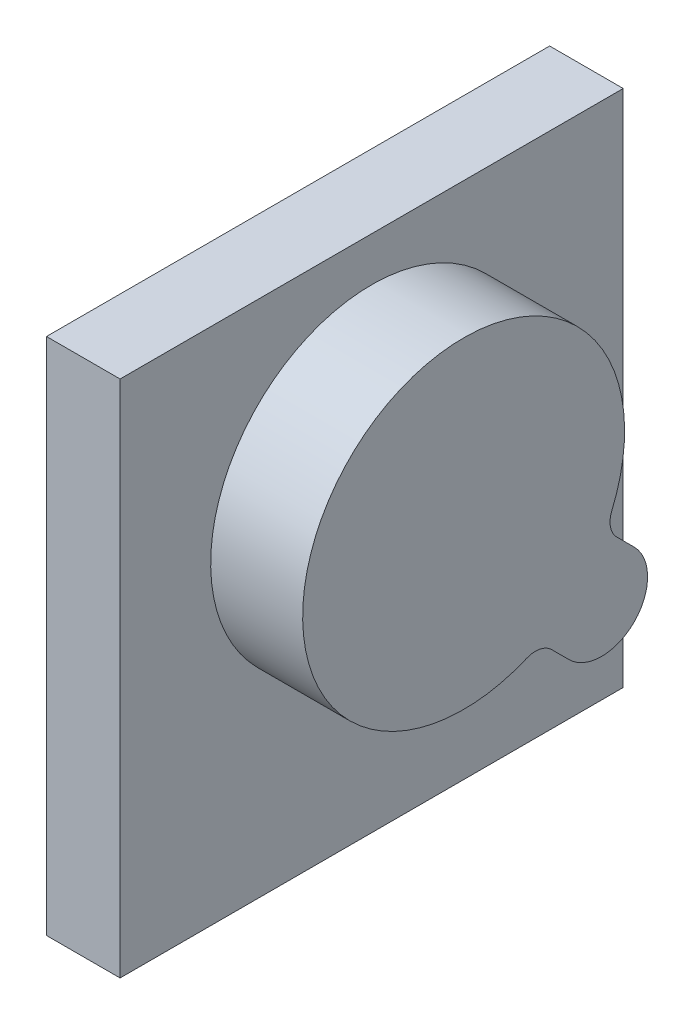
SolidWorks part; units mm, degrees
ref_plane "Front Plane" through (0, 0, 0) normal (0, 0, 1) x (1, 0, 0)
ref_plane "Top Plane" through (0, 0, 0) normal (0, 1, 0) x (1, 0, 0)
ref_plane "Right Plane" through (0, 0, 0) normal (1, 0, 0) x (0, 0, -1)
sketch "Sketch1" plane through (0, 0, 0) normal (1, 0, 0) x (0, 0, -1)
  line L1 (69.469, 71.628) -> (-69.469, 71.628)
  line L2 (69.469, 71.628) -> (69.469, -71.628)
  line L3 (69.469, -71.628) -> (-69.469, -71.628)
  line L4 (-69.469, 71.628) -> (-69.469, -71.628)
  line L5 (69.469, 71.628) -> (-69.469, -71.628) construction
  line L6 (69.469, -71.628) -> (-69.469, 71.628) construction
  point P0 (0, 0)
  dimension "D1" = 143.256
  dimension "D2" = 138.938
extrude "Boss-Extrude1" add sketch "Sketch1" against normal blind 20.32
sketch "Sketch2" plane through (0, 0, 0) normal (1, 0, 0) x (0, 0, -1)
  line L0 (-69.469, -71.628) -> (69.469, -71.628) construction
  line L1 (69.469, -41.656) -> (-69.469, -41.656)
  line L2 (69.469, -41.656) -> (69.469, 71.628)
  line L3 (69.469, 71.628) -> (-69.469, 71.628)
  line L4 (-69.469, -41.656) -> (-69.469, 71.628)
  line L5 (69.469, -41.656) -> (-69.469, 71.628) construction
  line L6 (69.469, 71.628) -> (-69.469, -41.656) construction
  line L7 (47.0803, -14.1337) -> (42.2799, -9.3334)
  line L8 (29.1197, -32.0943) -> (24.3194, -27.2939)
  arc A0 (40.9238, -2.3646) -> (17.3506, -25.9378) centre (0, 14.986) ccw
  arc A1 (47.0803, -14.1337) -> (29.1197, -32.0943) centre (38.1, -23.114) cw
  arc A2 (24.3194, -27.2939) -> (17.3506, -25.9378) centre (19.8293, -31.7841) ccw
  arc A3 (42.2799, -9.3334) -> (40.9238, -2.3646) centre (46.7701, -4.8433) cw
  point P0 (0, 14.986)
  dimension "D2" = 44.45
  dimension "D3" = 12.7
  dimension "D6" = 6.35
  dimension "D1" = 29.972
  dimension "D4" = 38.1
  dimension "D5" = 38.1
extrude "Boss-Extrude2" add sketch "Sketch2" along normal blind 25.4 contours L7 A3 A0 A2 L8 A1
